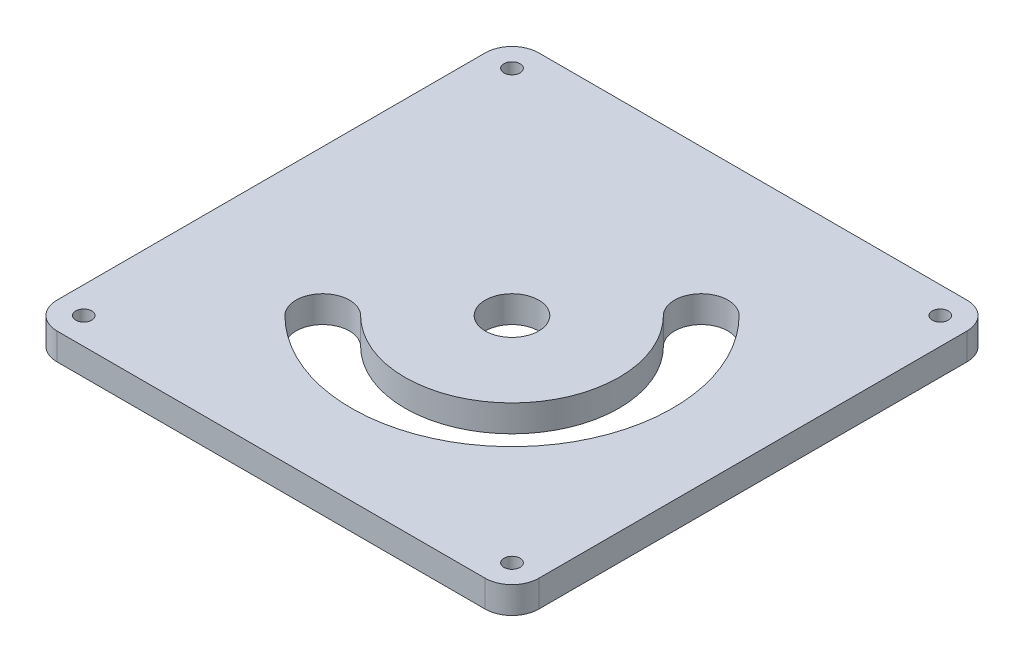
SolidWorks part; units mm, degrees
ref_plane "Front" through (0, 0, 0) normal (0, 0, 1) x (1, 0, 0)
ref_plane "Top" through (0, 0, 0) normal (0, 1, 0) x (1, 0, 0)
ref_plane "Right" through (0, 0, 0) normal (1, 0, 0) x (0, 0, -1)
sketch "Sketch1" plane through (0, 0, 0) normal (0, 1, 0) x (1, 0, 0)
  line L1 (-45, 45) -> (45, 45)
  line L2 (-45, 45) -> (-45, -45)
  line L3 (-45, -45) -> (45, -45)
  line L4 (45, 45) -> (45, -45)
  line L5 (-45, 45) -> (45, -45) construction
  line L6 (-45, -45) -> (45, 45) construction
  arc A0 (17.6777, 17.6777) -> (-17.6777, -17.6777) centre (0, 0) cw construction
  arc A1 (-21.2132, -21.2132) -> (21.2132, 21.2132) centre (0, 0) ccw
  arc A2 (-14.1421, -14.1421) -> (14.1421, 14.1421) centre (0, 0) ccw
  arc A3 (-14.1421, -14.1421) -> (-21.2132, -21.2132) centre (-17.6777, -17.6777) ccw
  arc A4 (21.2132, 21.2132) -> (14.1421, 14.1421) centre (17.6777, 17.6777) ccw
  circle A5 centre (0, 0) radius 5
  point P0 (0, 0)
  point P9 (17.6777, -17.6777)
  dimension "D2" = 25
  dimension "D3" = 5
  dimension "D4" = 10
  dimension "D1" = 90
extrude "Boss-Extrude1" add sketch "Sketch1" along normal blind 5
sketch "Sketch2" plane through (0, 5, 0) normal (0, 1, 0) x (1, 0, 0)
  line L1 (-40, -40) -> (40, -40) construction
  line L2 (-40, -40) -> (-40, 40) construction
  line L3 (-40, 40) -> (40, 40) construction
  line L4 (40, -40) -> (40, 40) construction
  line L5 (-40, -40) -> (40, 40) construction
  line L6 (-40, 40) -> (40, -40) construction
  circle A0 centre (-40, 40) radius 1.5
  circle A1 centre (40, 40) radius 1.5
  circle A2 centre (40, -40) radius 1.5
  circle A3 centre (-40, -40) radius 1.5
  point P0 (0, 0)
  dimension "D2" = 3
  dimension "D1" = 80
extrude "Cut-Extrude1" cut sketch "Sketch2" against normal through all
fillet "Fillet1" radius 5 4 edges at (-45, 2.5, 45) (-45, 2.5, -45) (45, 2.5, 45) (45, 2.5, -45)
